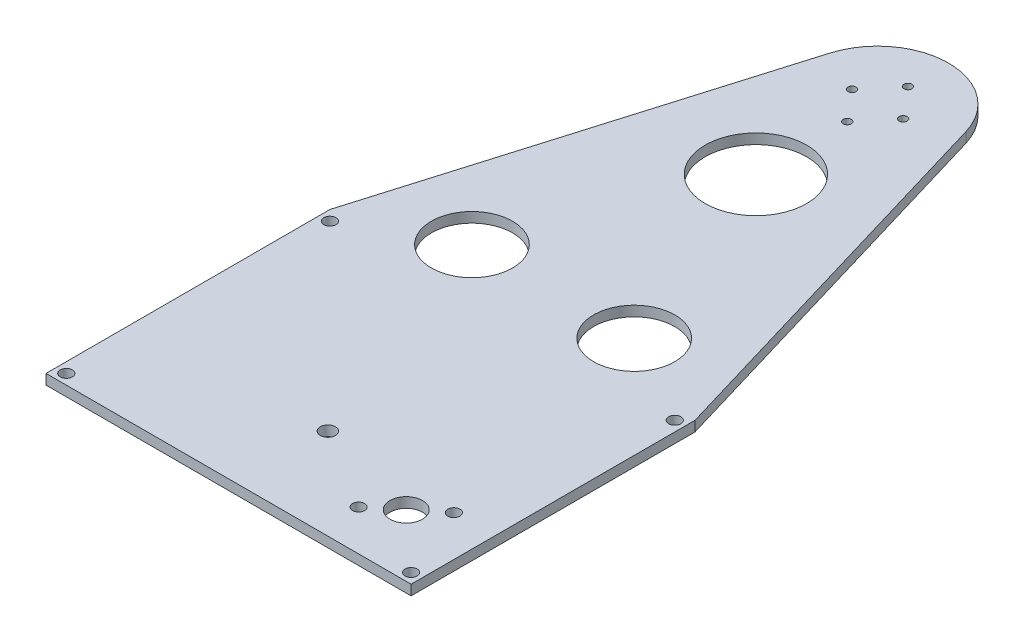
SolidWorks part; units mm, degrees
material "PLA/ABS"
ref_plane "Front Plane" through (0, 0, 0) normal (0, 0, 1) x (1, 0, 0)
ref_plane "Top Plane" through (0, 0, 0) normal (0, 1, 0) x (1, 0, 0)
ref_plane "Right Plane" through (0, 0, 0) normal (1, 0, 0) x (0, 0, -1)
other "Bounding Box"
ref_plane "Default Plane" through (-8.9266, -12.7485, 0) normal (-0.1736, 0.9848, 0) x (0.9848, 0.1736, 0)
sketch "Sketch1" plane through (0, 0, 0) normal (0, 1, 0) x (1, 0, 0)
  line L0 (0, 0) -> (0, -133.35) construction
  line L1 (0, -133.35) -> (-6.35, -133.35) construction
  line L2 (-63.5, -133.35) -> (-57.15, -133.35) construction
  line L3 (-57.15, -143.3195) -> (-6.35, -143.3195)
  line L4 (-57.15, -143.3195) -> (-57.15, -123.3805)
  line L5 (-57.15, -123.3805) -> (-6.35, -123.3805)
  line L6 (-6.35, -143.3195) -> (-6.35, -123.3805)
  line L7 (-57.15, -143.3195) -> (-6.35, -123.3805) construction
  line L8 (-57.15, -123.3805) -> (-6.35, -143.3195) construction
  line L9 (-88.9, -167.386) -> (-63.5, -167.386)
  line L10 (-88.9, -167.386) -> (-88.9, -99.314)
  line L11 (-88.9, -99.314) -> (-63.5, -99.314)
  line L12 (-63.5, -167.386) -> (-63.5, -99.314)
  line L13 (-88.9, -167.386) -> (-63.5, -99.314) construction
  line L14 (-88.9, -99.314) -> (-63.5, -167.386) construction
  line L15 (57.15, -123.3805) -> (6.35, -123.3805)
  line L16 (-50.8, -196.85) -> (6.35, -196.85)
  line L17 (-50.8, -196.85) -> (-50.8, -180.34)
  line L18 (-50.8, -180.34) -> (6.35, -180.34)
  line L19 (6.35, -196.85) -> (6.35, -180.34)
  line L20 (-50.8, -196.85) -> (6.35, -180.34) construction
  line L21 (-50.8, -180.34) -> (6.35, -196.85) construction
  line L22 (6.35, -143.3195) -> (6.35, -123.3805)
  line L23 (57.15, -143.3195) -> (6.35, -143.3195)
  line L24 (57.15, -143.3195) -> (57.15, -123.3805)
  line L25 (88.9, -99.314) -> (63.5, -99.314)
  line L26 (63.5, -167.386) -> (63.5, -99.314)
  line L27 (88.9, -167.386) -> (63.5, -167.386)
  line L28 (88.9, -167.386) -> (88.9, -99.314)
  line L30 (50.8, -196.85) -> (7.62, -196.85)
  line L31 (50.8, -196.85) -> (50.8, -176.7078)
  line L32 (50.8, -176.7078) -> (7.62, -176.7078)
  line L33 (7.62, -196.85) -> (7.62, -176.7078)
  line L34 (50.8, -196.85) -> (7.62, -176.7078) construction
  line L35 (50.8, -176.7078) -> (7.62, -196.85) construction
  line L36 (-57.15, -203.2) -> (57.15, -203.2)
  line L37 (-57.15, -203.2) -> (-57.15, -114.3)
  line L38 (-57.15, -114.3) -> (57.15, -114.3)
  line L39 (57.15, -203.2) -> (57.15, -114.3)
  line L40 (-57.15, -203.2) -> (57.15, -114.3) construction
  line L41 (-57.15, -114.3) -> (57.15, -203.2) construction
  circle A0 centre (0, 0) radius 38.1
  circle A1 centre (0, 0) radius 13.843
  point P3 (-22.225, -188.595)
  point P6 (-31.75, -133.35)
  point P12 (-76.2, -133.35)
  point P22 (0, -114.3)
  point P23 (0, -158.75)
  point P36 (0, -38.1)
  point P38 (29.21, -186.7789)
  dimension "D1" = 76.2
  dimension "D19" = 27.686
  dimension "D2" = 50.8
  dimension "D3" = 19.939
  dimension "D4" = 68.072
  dimension "D5" = 25.4
  dimension "D6" = 57.15
  dimension "D7" = 16.51
  dimension "D8" = 43.18
  dimension "D9" = 20.1422
  dimension "D10" = 114.3
  dimension "D11" = 114.3
  dimension "D12" = 19.05
  dimension "D13" = 6.35
  dimension "D14" = 6.35
  dimension "D15" = 6.35
  dimension "D16" = 6.35
  dimension "D17" = 88.9
  dimension "D18" = 6.35
sketch "Sketch2" plane through (0, 0, 0) normal (1, 0, 0) x (0, 0, -1)
  line L1 (-203.2, 12.7) -> (-114.3, 12.7)
  line L2 (-203.2, 12.7) -> (-203.2, -12.7)
  line L3 (-203.2, -12.7) -> (-114.3, -12.7)
  line L4 (-114.3, 12.7) -> (-114.3, -12.7)
  line L5 (-203.2, 12.7) -> (-114.3, -12.7) construction
  line L6 (-203.2, -12.7) -> (-114.3, 12.7) construction
  line L7 (-203.2, 12.7) -> (12.7, 12.7)
  line L8 (-203.2, 12.7) -> (-203.2, 15.875)
  line L9 (-203.2, 15.875) -> (12.7, 15.875)
  line L10 (12.7, 12.7) -> (12.7, 15.875)
  line L11 (-203.2, 12.7) -> (12.7, 15.875) construction
  line L12 (-203.2, 15.875) -> (12.7, 12.7) construction
  line L13 (-203.2, -12.7) -> (-114.3, -12.7)
  line L14 (-203.2, -12.7) -> (-203.2, -15.875)
  line L15 (-203.2, -15.875) -> (-114.3, -15.875)
  line L16 (-114.3, -12.7) -> (-114.3, -15.875)
  line L17 (-203.2, -12.7) -> (-114.3, -15.875) construction
  line L18 (-203.2, -15.875) -> (-114.3, -12.7) construction
  circle A0 centre (-133.35, 0) radius 34.036
  point P4 (-167.386, 0)
  point P5 (-158.75, 0)
  point P15 (-95.25, 14.2875)
  point P19 (-158.75, -14.2875)
  dimension "D1" = 25.4
  dimension "D2" = 3.175
  dimension "D3" = 12.7
sketch "Sketch3" plane through (0, 0, 0) normal (0, 1, 0) x (1, 0, 0)
  line L1 (-57.15, -203.2) -> (57.15, -203.2)
  line L2 (-57.15, -203.2) -> (-57.15, -114.3)
  line L3 (-57.15, -114.3) -> (57.15, -114.3)
  line L4 (57.15, -203.2) -> (57.15, -114.3)
  line L5 (-57.15, -203.2) -> (57.15, -114.3) construction
  line L6 (-57.15, -114.3) -> (57.15, -203.2) construction
  line L7 (-50.8, -120.65) -> (50.8, -120.65)
  line L8 (-50.8, -120.65) -> (-50.8, -196.85)
  line L9 (-50.8, -196.85) -> (50.8, -196.85)
  line L10 (50.8, -120.65) -> (50.8, -196.85)
  line L11 (-50.8, -120.65) -> (50.8, -196.85) construction
  line L12 (-50.8, -196.85) -> (50.8, -120.65) construction
  point P0 (0, -158.75)
  point P7 (0, -158.75)
extrude "Boss-Extrude1" add sketch "Sketch3" along normal up to vertex (12.7 mm away) and the other way up to vertex (12.7 mm away) up to point (0, 12.7, 203.2) other way up to point (0, -12.7, 203.2)
sketch "Sketch4" plane through (0, -12.7, 0) normal (0, -1, 0) x (1, 0, 0)
  line L1 (-57.15, 203.2) -> (57.15, 203.2)
  line L2 (-57.15, 203.2) -> (-57.15, 114.3)
  line L3 (-57.15, 114.3) -> (57.15, 114.3)
  line L4 (57.15, 203.2) -> (57.15, 114.3)
  line L5 (-57.15, 203.2) -> (57.15, 114.3) construction
  line L6 (-57.15, 114.3) -> (57.15, 203.2) construction
  point P0 (0, 158.75)
extrude "Boss-Extrude2" add sketch "Sketch4" along normal up to vertex (3.175 mm away) up to point (0, -15.875, 203.2)
sketch "Sketch5" plane through (0, 12.7, 0) normal (0, 1, 0) x (1, 0, 0)
  line L0 (-21.3043, 6.3306) -> (-57.15, -114.3)
  line L1 (-57.15, -114.3) -> (-57.15, -203.2)
  line L2 (-57.15, -203.2) -> (57.15, -203.2)
  line L3 (57.15, -203.2) -> (57.15, -114.3)
  line L4 (57.15, -114.3) -> (21.3043, 6.3306)
  arc A0 (-21.3043, 6.3306) -> (21.3043, 6.3306) centre (0, 0) cw
  dimension "D1" = 22.225
extrude "Boss-Extrude3" add sketch "Sketch5" along normal up to vertex (3.175 mm away) separate body up to point (0, 15.875, 203.2)
sketch "Sketch7" plane through (0, -12.7, 0) normal (0, 1, 0) x (1, 0, 0)
  line L0 (-6.35, -143.3195) -> (-6.35, -123.3805) construction
  line L1 (-50.8, -120.65) -> (-6.35, -120.65)
  line L2 (-50.8, -120.65) -> (-50.8, -146.05)
  line L3 (-50.8, -146.05) -> (-6.35, -146.05)
  line L4 (-6.35, -120.65) -> (-6.35, -146.05)
  line L5 (-50.8, -120.65) -> (-6.35, -146.05) construction
  line L6 (-50.8, -146.05) -> (-6.35, -120.65) construction
  line L7 (50.8, -120.65) -> (6.35, -120.65)
  line L8 (50.8, -120.65) -> (50.8, -146.05)
  line L9 (50.8, -146.05) -> (6.35, -146.05)
  line L10 (6.35, -120.65) -> (6.35, -146.05)
  line L11 (50.8, -120.65) -> (6.35, -146.05) construction
  line L12 (50.8, -146.05) -> (6.35, -120.65) construction
  line L13 (6.35, -143.3195) -> (6.35, -123.3805) construction
  line L14 (0, -133.35) -> (-6.35, -133.35) construction
  point P4 (-28.575, -133.35)
  point P10 (28.575, -133.35)
extrude "Boss-Extrude4" add sketch "Sketch7" along normal blind 6.35
sketch "Sketch6" plane through (-57.15, 0, 0) normal (-1, 0, 0) x (0, 0, 1)
  circle A0 centre (133.35, 0) radius 9.9695
extrude "Cut-Extrude1" cut sketch "Sketch6" against normal through all
ref_plane "Plane1" through (0, 0, 0) normal (1, 0, 0) x (0, 0, -1)
sketch "Sketch13" plane through (0, -12.7, 0) normal (0, 1, 0) x (1, 0, 0)
  line L0 (-50.8, -146.05) -> (-6.35, -146.05) construction
  line L1 (-6.35, -120.65) -> (-35.56, -120.65)
  line L2 (-6.35, -120.65) -> (-6.35, -146.05)
  line L3 (-6.35, -146.05) -> (-35.56, -146.05)
  line L4 (-35.56, -120.65) -> (-35.56, -146.05)
  line L5 (-6.35, -120.65) -> (-35.56, -146.05) construction
  line L6 (-6.35, -146.05) -> (-35.56, -120.65) construction
  line L7 (-50.8, -120.65) -> (-50.8, -125.6644) construction
  line L9 (0, -55) -> (0, 55) construction
  line L10 (35.56, -120.65) -> (35.56, -146.05)
  line L11 (6.35, -146.05) -> (35.56, -146.05)
  line L12 (6.35, -120.65) -> (6.35, -146.05)
  line L13 (6.35, -120.65) -> (35.56, -120.65)
  point P4 (-20.955, -133.35)
  dimension "D1" = 15.24
extrude "Boss-Extrude5" add sketch "Sketch13" along normal blind 4.064
sketch "Sketch14" plane through (0, 0, 146.05) normal (0, 0, 1) x (1, 0, 0)
  line L0 (-35.56, -8.0762) -> (-35.56, -11.2291) construction
  line L1 (-30.48, -9.144) -> (-24.13, -9.144)
  line L2 (-30.48, -9.144) -> (-30.48, -11.684)
  line L3 (-30.48, -11.684) -> (-24.13, -11.684)
  line L4 (-24.13, -9.144) -> (-24.13, -11.684)
  line L5 (-30.48, -9.144) -> (-24.13, -11.684) construction
  line L6 (-30.48, -11.684) -> (-24.13, -9.144) construction
  line L7 (-35.56, -8.636) -> (-35.56, -9.9695) construction
  line L8 (-6.35, -6.35) -> (-50.8, -6.35) construction
  line L9 (-30.48, -5.08) -> (-24.13, -5.08)
  line L10 (-30.48, -5.08) -> (-30.48, -2.54)
  line L11 (-30.48, -2.54) -> (-24.13, -2.54)
  line L12 (-24.13, -5.08) -> (-24.13, -2.54)
  line L13 (-30.48, -5.08) -> (-24.13, -2.54) construction
  line L14 (-30.48, -2.54) -> (-24.13, -5.08) construction
  line L15 (-50.8, -12.7) -> (-6.35, -12.7) construction
  line L16 (0, -55) -> (0, 55) construction
  line L17 (30.48, -11.684) -> (24.13, -11.684)
  line L18 (24.13, -9.144) -> (24.13, -11.684)
  line L19 (30.48, -9.144) -> (24.13, -9.144)
  line L20 (30.48, -9.144) -> (30.48, -11.684)
  line L21 (30.48, -2.54) -> (24.13, -2.54)
  line L22 (24.13, -5.08) -> (24.13, -2.54)
  line L23 (30.48, -5.08) -> (24.13, -5.08)
  line L24 (30.48, -5.08) -> (30.48, -2.54)
  point P4 (-27.305, -10.414)
  point P13 (-27.305, -3.81)
  dimension "D1" = 2.54
  dimension "D2" = 6.35
  dimension "D3" = 5.08
  dimension "D4" = 1.27
  dimension "D5" = 1.016
extrude "Cut-Extrude2" cut sketch "Sketch14" against normal up to surface (31.75 mm away) up to face at (0, -1.5875, 114.3)
sketch "Sketch18" plane through (0, 0, 120.65) normal (0, 0, 1) x (1, 0, 0)
  line L0 (50.8, 12.7) -> (-50.8, 12.7) construction
  line L1 (-48.26, 12.7) -> (-38.1, 12.7)
  line L2 (-48.26, 12.7) -> (-48.26, 7.62)
  line L3 (-48.26, 7.62) -> (-38.1, 7.62)
  line L4 (-38.1, 12.7) -> (-38.1, 7.62)
  line L5 (-48.26, 12.7) -> (-38.1, 7.62) construction
  line L6 (-48.26, 7.62) -> (-38.1, 12.7) construction
  line L7 (-50.8, 12.7) -> (-50.8, -6.35) construction
  point P4 (-43.18, 10.16)
  dimension "D1" = 10.16
  dimension "D2" = 2.54
  dimension "D3" = 5.08
extrude "Cut-Extrude3" cut sketch "Sketch18" against normal up to surface (6.35 mm away) up to face at (-27.305, -3.81, 114.3)
sketch "Sketch19" plane through (0, 12.7, 0) normal (0, 1, 0) x (1, 0, 0)
  line L0 (-57.15, -114.3) -> (-57.15, -203.2) construction
  line L1 (-48.26, -114.3) -> (-57.15, -114.3) construction
  line L2 (-50.8, -120.65) -> (-50.8, -196.85) construction
  line L5 (57.15, -203.2) -> (57.15, -114.3) construction
  line L6 (57.15, -114.3) -> (-38.1, -114.3) construction
  line L7 (-57.15, -203.2) -> (57.15, -203.2) construction
  line L8 (-50.8, -196.85) -> (50.8, -196.85) construction
  circle A0 centre (-53.975, -117.475) radius 3.175 construction
  circle A1 centre (-53.975, -117.475) radius 0.635
  circle A2 centre (53.975, -117.475) radius 3.175 construction
  circle A3 centre (53.975, -117.475) radius 0.635
  circle A4 centre (-53.975, -200.025) radius 3.175 construction
  circle A5 centre (-53.975, -200.025) radius 0.635
  circle A6 centre (53.975, -200.025) radius 3.175 construction
  circle A7 centre (53.975, -200.025) radius 0.635
  dimension "D1" = 1.27
  dimension "D2" = 6.35
extrude "Cut-Extrude4" cut sketch "Sketch19" against normal blind 25.4
sketch "Sketch20" plane through (0, 15.875, 0) normal (0, 1, 0) x (1, 0, 0)
  circle A0 centre (-53.975, -117.475) radius 1.905
  circle A1 centre (-53.975, -200.025) radius 1.905
  circle A2 centre (53.975, -200.025) radius 1.905
  circle A3 centre (53.975, -117.475) radius 1.905
  dimension "D1" = 3.81
  dimension "D2" = 3.81
  dimension "D3" = 3.81
  dimension "D4" = 3.81
extrude "Cut-Extrude7" cut sketch "Sketch20" against normal up to surface (3.175 mm away) up to face at (0, 12.7, 101.0741)
sketch "Sketch23" plane through (0, 15.875, 0) normal (0, 1, 0) x (1, 0, 0)
  line L0 (-57.15, -203.2) -> (57.15, -203.2) construction
  line L1 (44.45, -177.1085) -> (28.015, -177.1085) construction
  line L2 (44.45, -177.1085) -> (44.45, -190.5) construction
  line L3 (44.45, -190.5) -> (28.015, -190.5) construction
  line L4 (28.015, -177.1085) -> (28.015, -190.5) construction
  line L5 (44.45, -177.1085) -> (28.015, -190.5) construction
  line L6 (44.45, -190.5) -> (28.015, -177.1085) construction
  line L7 (57.15, -203.2) -> (57.15, -114.3) construction
  circle A0 centre (36.2325, -183.8043) radius 5.08
  circle A1 centre (44.45, -177.1085) radius 1.905
  circle A2 centre (28.015, -190.5) radius 1.905
  circle A4 centre (2.615, -174.7273) radius 2.3812
  point P0 (36.2325, -183.8043)
  dimension "D1" = 10.16
  dimension "D2" = 3.81
  dimension "D3" = 10.6
  dimension "D4" = 12.7
  dimension "D7" = 4.7625
  dimension "D8" = 25.4
  dimension "D5" = 12.7
  dimension "D6" = 13.3915
extrude "Cut-Extrude8" cut sketch "Sketch23" against normal up to surface (3.175 mm away) up to face at (53.975, 12.7, 115.57)
sketch "Sketch24" plane through (0, 15.875, 0) normal (0, 1, 0) x (1, 0, 0)
  circle A0 centre (0, 0) radius 8 construction
  circle A1 centre (0, 0) radius 9.5 construction
  circle A2 centre (0, 9.5) radius 1.25
  circle A3 centre (0, -9.5) radius 1.25
  circle A4 centre (-8, 0) radius 1.25
  circle A5 centre (8, 0) radius 1.25
  dimension "D1" = 19
  dimension "D2" = 16
  dimension "D3" = 2.5
  dimension "D4" = 2.5
  dimension "D5" = 2.5
  dimension "D6" = 2.5
extrude "Cut-Extrude9" cut sketch "Sketch24" against normal up to surface (3.175 mm away) up to face at (2.615, 12.7, 172.346)
sketch "Sketch26" plane through (57.15, 0, 0) normal (1, 0, 0) x (0, 0, -1)
  line L0 (-203.2, 12.7) -> (-203.454, 12.7)
  line L1 (-203.454, 12.7) -> (-203.454, 15.875)
  line L2 (-203.454, 15.875) -> (-204.724, 15.875)
  line L3 (-204.724, 15.875) -> (-213.2314, -15.875)
  line L4 (-213.2314, -15.875) -> (-203.2, -15.875)
  line L6 (-203.2, -15.875) -> (-203.2, 12.7)
  line L7 (-265.8932, -34.036) -> (49734.1068, -34.036) construction
  line L8 (-203.2, 15.875) -> (12.7, 15.875) construction
  circle A0 centre (-133.35, 0) radius 34.036 construction
  dimension "D2" = 0.254
  dimension "D3" = 75
  dimension "D4" = 1.27
extrude "Boss-Extrude7" add sketch "Sketch26" against normal up to surface (114.3 mm away) up to face at (-57.15, 0, 143.3195)
sketch "Sketch27" plane through (0, -15.875, 0) normal (0, -1, 0) x (1, 0, 0)
  line L0 (57.15, 171.45) -> (95.25, 171.45)
  line L1 (57.15, 203.2) -> (57.15, 114.3) construction
  line L2 (95.25, 171.45) -> (95.25, 128.27)
  line L3 (95.25, 128.27) -> (100.33, 128.27)
  line L4 (100.33, 128.27) -> (100.33, 176.5362)
  line L5 (100.33, 176.5362) -> (57.15, 184.15)
  line L6 (57.15, 184.15) -> (57.15, 171.45)
  line L7 (57.15, 143.3195) -> (57.15, 123.3805) construction
  line L8 (0, 133.35) -> (-6.35, 133.35) construction
  line L9 (0, 0) -> (0, 227.7127) construction
  line L10 (-100.33, 176.5362) -> (-57.15, 184.15)
  line L11 (-100.33, 128.27) -> (-100.33, 176.5362)
  line L12 (-95.25, 128.27) -> (-100.33, 128.27)
  line L13 (-95.25, 171.45) -> (-95.25, 128.27)
  line L14 (-57.15, 171.45) -> (-95.25, 171.45)
  line L15 (-57.15, 184.15) -> (-57.15, 171.45)
  dimension "D1" = 38.1
  dimension "D2" = 5.08
  dimension "D3" = 5.08
  dimension "D4" = 38.1
  dimension "D5" = 10
  dimension "D6" = 12.7
extrude "Boss-Extrude8" add sketch "Sketch27" against normal up to surface (28.575 mm away) up to face at (0, 12.7, -10.75)
sketch "Sketch25" plane through (0, 15.875, 0) normal (0, 1, 0) x (1, 0, 0)
  line L0 (-25.4, -101.6) -> (0, -38.1) construction
  line L1 (0, -38.1) -> (25.4, -101.6) construction
  line L2 (25.4, -101.6) -> (-25.4, -101.6) construction
  line L3 (0, -101.6) -> (0, 0) construction
  line L4 (-57.15, -114.3) -> (57.15, -114.3) construction
  circle A0 centre (0, -38.1) radius 15.875
  circle A1 centre (-25.4, -101.6) radius 12.7
  circle A2 centre (25.4, -101.6) radius 12.7
  arc A3 (21.3043, 6.3306) -> (-21.3043, 6.3306) centre (0, 0) ccw construction
  dimension "D1" = 31.75
  dimension "D2" = 25.4
  dimension "D3" = 50.8
extrude "Cut-Extrude10" cut sketch "Sketch25" against normal through all
fillet "Fillet1" radius 9.525 6 edges at (57.15, -1.5875, 184.15) (100.33, -1.5875, 176.5362) (95.25, -1.5875, 171.45) (-100.33, -1.5875, 176.5362) (-57.15, -1.5875, 184.15) (-95.25, -1.5875, 171.45)
fillet "Fillet2" radius 5.08 2 edges at (57.15, -1.5875, 171.45) (-57.15, -1.5875, 171.45)
fillet "Fillet3" radius 9.525 4 edges at (-97.79, 12.7, 128.27) (-97.79, -15.875, 128.27) (97.79, 12.7, 128.27) (97.79, -15.875, 128.27)
delete or keep bodies "Body-Delete/Keep 1" type delete bodies bodies 121
delete or keep bodies "Body-Delete/Keep 2" [suppressed] type delete bodies bodies 118
